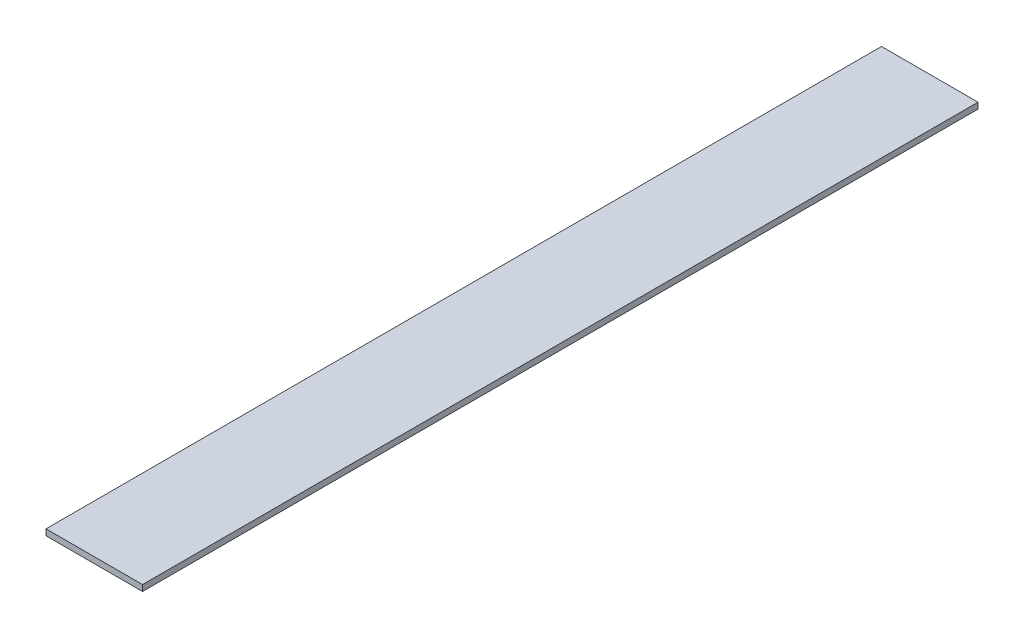
SolidWorks part; units mm, degrees
ref_plane "Front Plane" through (0, 0, 0) normal (0, 0, 1) x (1, 0, 0)
ref_plane "Top Plane" through (0, 0, 0) normal (0, 1, 0) x (1, 0, 0)
ref_plane "Right Plane" through (0, 0, 0) normal (1, 0, 0) x (0, 0, -1)
sketch "Sketch1" plane through (0, 0, 0) normal (0, 1, 0) x (1, 0, 0)
  line L1 (-25.4, 219.8688) -> (25.4, 219.8688)
  line L2 (-25.4, 219.8688) -> (-25.4, -219.8688)
  line L3 (-25.4, -219.8688) -> (25.4, -219.8688)
  line L4 (25.4, 219.8688) -> (25.4, -219.8688)
  line L5 (-25.4, 219.8688) -> (25.4, -219.8688) construction
  line L6 (-25.4, -219.8688) -> (25.4, 219.8688) construction
  point P0 (0, 0)
  dimension "D1" = 50.8
  dimension "D2" = 439.7375
extrude "Boss-Extrude1" add sketch "Sketch1" along normal blind 3.175
